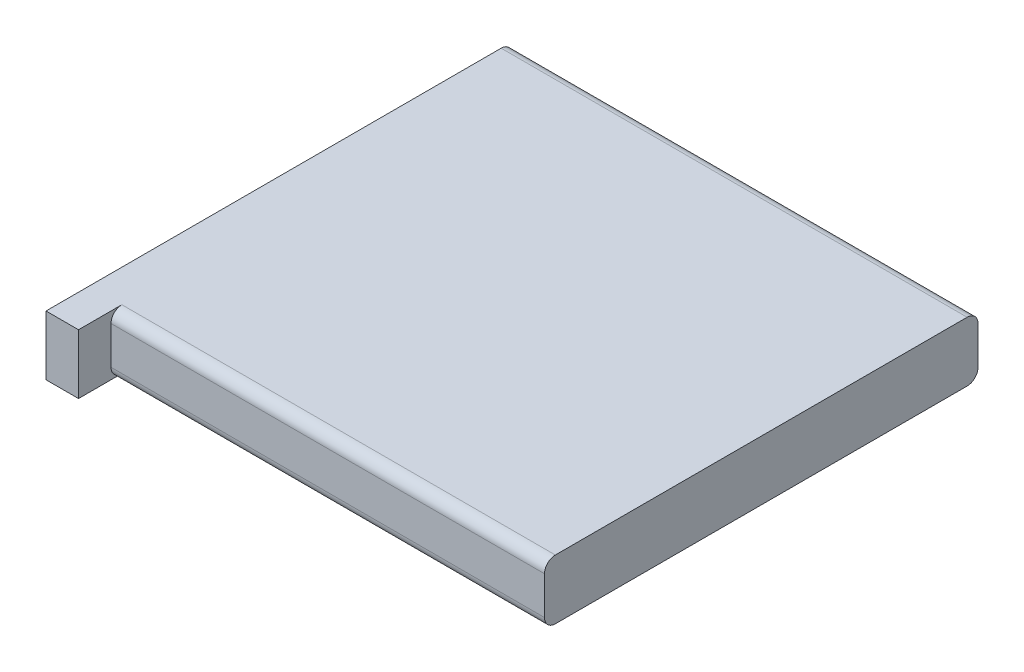
SolidWorks part; units mm, degrees
ref_plane "Front Plane" through (0, 0, 0) normal (0, 0, 1) x (1, 0, 0)
ref_plane "Top Plane" through (0, 0, 0) normal (0, 1, 0) x (1, 0, 0)
ref_plane "Right Plane" through (0, 0, 0) normal (1, 0, 0) x (0, 0, -1)
sketch "Sketch1" plane through (0, 0, 0) normal (0, 1, 0) x (1, 0, 0)
  line L1 (21.5, -20) -> (-21.5, -20)
  line L2 (21.5, -20) -> (21.5, 20)
  line L3 (21.5, 20) -> (-21.5, 20)
  line L4 (-21.5, -20) -> (-21.5, 20)
  line L5 (21.5, -20) -> (-21.5, 20) construction
  line L6 (21.5, 20) -> (-21.5, -20) construction
  point P0 (0, 0)
  dimension "D1" = 43
  dimension "D2" = 40
extrude "Boss-Extrude1" add sketch "Sketch1" along normal blind 5.5
fillet "Fillet1" radius 1 4 edges at (0, 0, -20) (0, 5.5, -20) (0, 0, 20) (0, 5.5, 20)
sketch "Sketch2" plane through (0, 0, 20) normal (0, 0, 1) x (1, 0, 0)
  line L0 (21.5, 0) -> (-21.5, 0) construction
  line L1 (-21.5, 5.5) -> (-18.5, 5.5)
  line L2 (-21.5, 5.5) -> (-21.5, 0)
  line L3 (-21.5, 0) -> (-18.5, 0)
  line L4 (-18.5, 5.5) -> (-18.5, 0)
  dimension "D1" = 3
extrude "Boss-Extrude2" add sketch "Sketch2" along normal blind 3 and the other way blind 3
